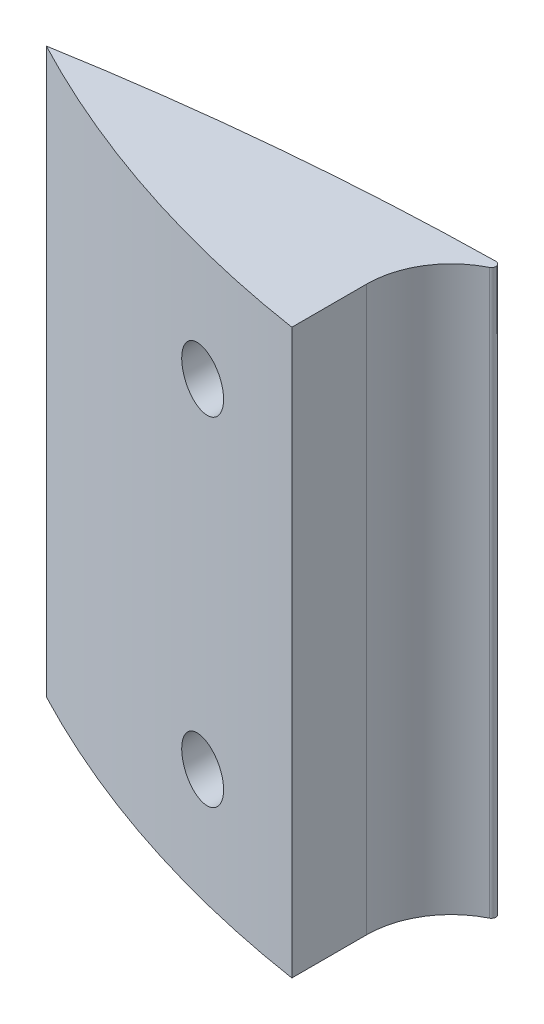
SolidWorks part; units mm, degrees
material "Hexcel AS4C (3000 Filaments)"
ref_plane "Front Plane" through (0, 0, 0) normal (0, 0, 1) x (1, 0, 0)
ref_plane "Top Plane" through (0, 0, 0) normal (0, 1, 0) x (1, 0, 0)
ref_plane "Right Plane" through (0, 0, 0) normal (1, 0, 0) x (0, 0, -1)
sketch "Sketch1" plane through (0, 0, 0) normal (0, 1, 0) x (1, 0, 0)
  line L0 (0, 0) -> (0, 65.0875)
  line L5 (-4.7625, 144.4625) -> (-4.7625, 140.2442)
  arc A0 (-2.2375, 149.2082) -> (-25.4, 147.0474) centre (0, 0) ccw
  arc A1 (-2.1206, 148.7268) -> (-4.7625, 144.4625) centre (0, 144.4625) ccw
  arc A3 (-25.4, 147.0474) -> (-4.7625, 140.2442) centre (5.3568, 205.6442) ccw
  arc A4 (-2.2375, 149.2082) -> (-2.1206, 148.7268) centre (-2.2337, 148.9543) cw
  dimension "D1" = 9.525
  dimension "D2" = 149.225
  dimension "D4" = 0.254
  dimension "D3" = 25.4
extrude "Boss-Extrude1" add sketch "Sketch1" along normal blind 31.75 contours A0 A3 L5 A1
ref_plane "Plane1" through (0, 0, -149.225) normal (0, 0, -1) x (-1, 0, 0)
sketch "Sketch2" plane through (0, 0, -149.225) normal (0, 0, -1) x (-1, 0, 0)
  line L0 (0, 31.75) -> (4.7625, 31.75)
  line L4 (2.2375, 0) -> (25.4, 0)
  line L6 (25.4, 0) -> (25.4, 31.75)
  line L12 (2.2375, 0) -> (25.4, 0)
  line L19 (25.4, 0) -> (25.4, 31.75)
  line L20 (25.4, 31.75) -> (2.2375, 31.75)
  line L22 (25.4, 31.75) -> (2.2375, 31.75)
  line L23 (2.2375, 31.75) -> (2.2375, 0)
  line L24 (2.2375, 31.75) -> (2.2375, 0)
  circle A0 centre (11.1125, 25.4) radius 1.5875
  circle A1 centre (11.1125, 6.35) radius 1.5875
  dimension "D2" = 4.7625
  dimension "D3" = 3.175
  dimension "D6" = 3.175
  dimension "D4" = 6.35
  dimension "D8" = 6.35
  dimension "D1" = 0
extrude "Cut-Extrude1" cut sketch "Sketch2" against normal through all contours A0 | A1
